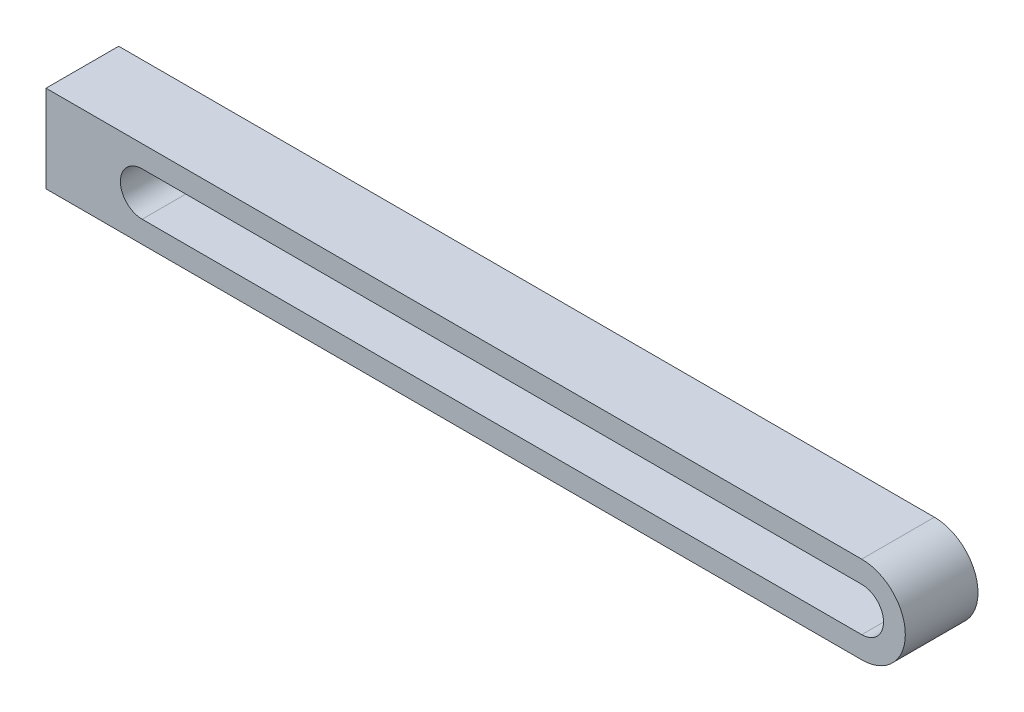
SolidWorks part; units mm, degrees
ref_plane "Front Plane" through (0, 0, 0) normal (0, 0, 1) x (1, 0, 0)
ref_plane "Top Plane" through (0, 0, 0) normal (0, 1, 0) x (1, 0, 0)
ref_plane "Right Plane" through (0, 0, 0) normal (1, 0, 0) x (0, 0, -1)
sketch "Sketch2" plane through (0, 0, 0) normal (0, 0, 1) x (1, 0, 0)
  line L0 (0, 0) -> (49.5, 0) construction
  line L1 (0, 3) -> (49.5, 3)
  line L2 (49.5, -3) -> (3, -3)
  line L3 (0, -1.5) -> (49.5, -1.5)
  line L4 (49.5, 1.5) -> (0, 1.5)
  line L6 (0, 3) -> (-6.6168, 3)
  line L8 (3, -3) -> (-6.6168, -3)
  line L9 (-6.6168, 3) -> (-6.6168, -3)
  arc A0 (0, 1.5) -> (0, -1.5) centre (0, 0) ccw
  arc A1 (49.5, -1.5) -> (49.5, 1.5) centre (49.5, 0) ccw
  arc A3 (49.5, -3) -> (49.5, 3) centre (49.5, 0) ccw
  dimension "D1" = 3
  dimension "D2" = 3
  dimension "D4" = 6
  dimension "D5" = 49.5
extrude "Boss-Extrude1" add sketch "Sketch2" along normal blind 5
